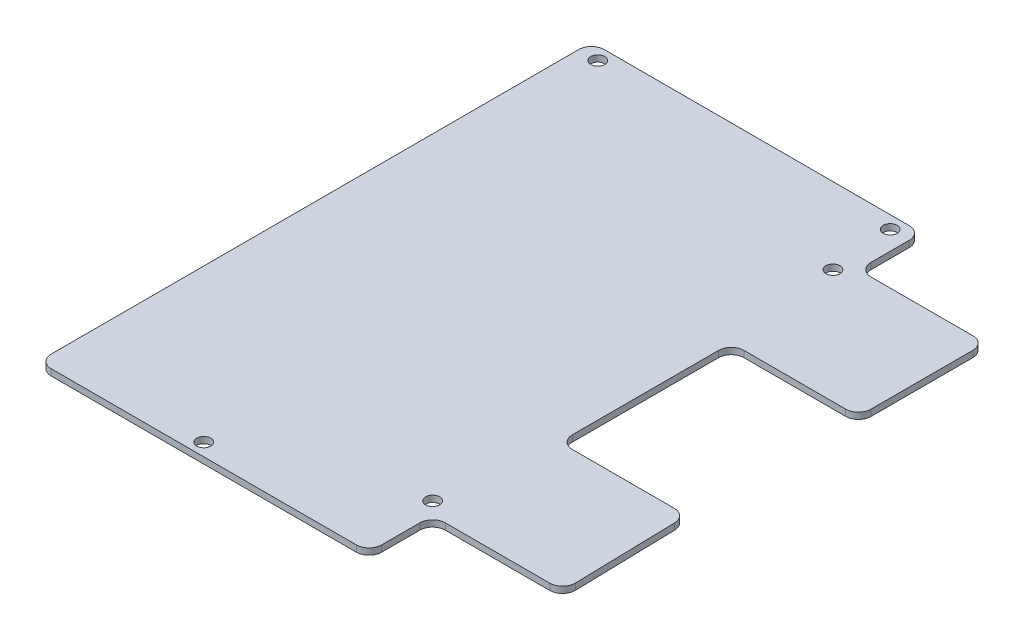
SolidWorks part; units mm, degrees
ref_plane "Front Plane" through (0, 0, 0) normal (0, 0, 1) x (1, 0, 0)
ref_plane "Top Plane" through (0, 0, 0) normal (0, 1, 0) x (1, 0, 0)
ref_plane "Right Plane" through (0, 0, 0) normal (1, 0, 0) x (0, 0, -1)
sketch "Sketch1" plane through (0, 0, 0) normal (0, 1, 0) x (1, 0, 0)
  line L0 (51.6637, 77) -> (51.6637, 87)
  line L1 (-0.3363, 0) -> (51.6637, 0)
  line L2 (-0.3363, 0) -> (-0.3363, 87)
  line L3 (-0.3363, 87) -> (51.6637, 87)
  line L4 (51.6637, 0) -> (51.6637, 10.0028)
  line L5 (51.6637, 77) -> (71.6637, 77)
  line L6 (51.6637, 57) -> (71.6637, 57)
  line L7 (71.6637, 77) -> (71.6637, 57)
  line L8 (51.6637, 30) -> (51.6637, 57)
  line L9 (51.6637, 10.0028) -> (72.1535, 10.004)
  line L10 (72.1535, 10.004) -> (71.6637, 29.998)
  line L11 (51.6637, 30) -> (71.6637, 29.998)
  dimension "D1" = 52
  dimension "D2" = 87
  dimension "D3" = 20
  dimension "D4" = 20
  dimension "D5" = 10
  dimension "D6" = 20
  dimension "D7" = 20
  dimension "D8" = 10.0028
  dimension "D9" = 27
extrude "Boss-Extrude1" add sketch "Sketch1" along normal blind 1
sketch "Sketch2" plane through (0, 0, 0) normal (0, -1, 0) x (1, 0, 0)
  line L0 (51.6637, -87) -> (-0.3363, -87) construction
  line L1 (-0.3363, -87) -> (-0.3363, 0) construction
  line L2 (51.6637, -77) -> (51.6637, -87) construction
  line L3 (-0.3363, 0) -> (51.6637, 0) construction
  line L4 (51.6637, 0) -> (51.6637, -10.0028) construction
  line L5 (51.6637, -10.0028) -> (72.1535, -10.004) construction
  line L6 (71.6637, -77) -> (51.6637, -77) construction
  circle A0 centre (2.6637, -85) radius 1.1
  circle A1 centre (48.6637, -85) radius 1.1
  circle A2 centre (23.6637, -2) radius 1.1
  circle A3 centre (49.6637, -12.0026) radius 1.1
  circle A5 centre (49.6637, -75) radius 1.1
  dimension "D1" = 2
  dimension "D4" = 2
  dimension "D6" = 2
  dimension "D8" = 2
  dimension "D2" = 3
  dimension "D3" = 3
  dimension "D5" = 24
  dimension "D7" = 2
  dimension "D9" = 2
extrude "Cut-Extrude1" cut sketch "Sketch2" against normal blind 4
fillet "Fillet1" radius 2 12 edges at (-0.3363, 0.5, -87) (51.6637, 0.5, -87) (51.6637, 0.5, -77) (71.6637, 0.5, -77) (71.6637, 0.5, -57) (51.6637, 0.5, -57) (51.6637, 0.5, -30) (71.6637, 0.5, -29.998) (72.1535, 0.5, -10.004) (51.6637, 0.5, -10.0028) (51.6637, 0.5, 0) (-0.3363, 0.5, 0)
